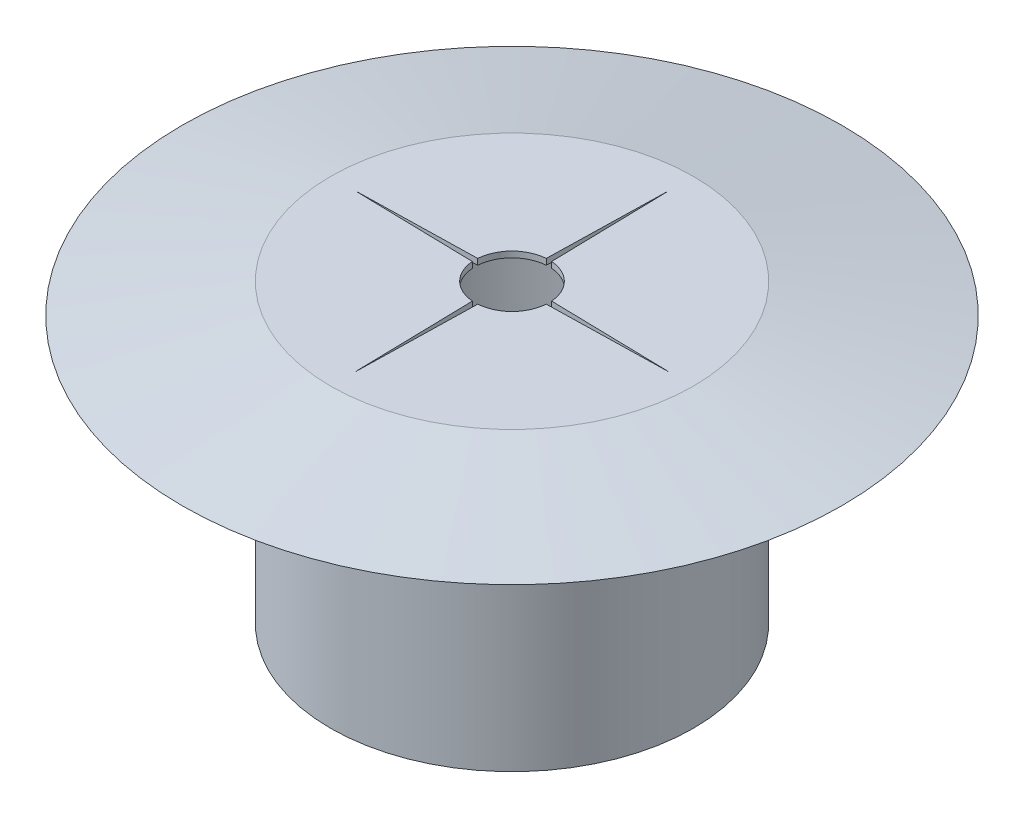
SolidWorks part; units mm, degrees
ref_plane "Alzado" through (0, 0, 0) normal (0, 0, 1) x (1, 0, 0)
ref_plane "Planta" through (0, 0, 0) normal (0, 1, 0) x (1, 0, 0)
ref_plane "Vista lateral" through (0, 0, 0) normal (1, 0, 0) x (0, 0, -1)
sketch "Croquis1" plane through (0, 0, 0) normal (0, 0, 1) x (1, 0, 0)
  line L0 (0, 0) -> (0, 16.2) construction
  line L1 (-10.9, 20) -> (-10.9, 0)
  line L2 (-10.9, 0) -> (-12.25, 0)
  line L3 (-12.25, 0) -> (-12.25, 18)
  line L4 (-12.25, 18) -> (-22.25, 18)
  line L5 (-22.25, 18) -> (-12.25, 20)
  line L6 (-12.25, 20) -> (-10.9, 20)
  dimension "D1" = 1.35
  dimension "D2" = 2
  dimension "D3" = 12.25
  dimension "D4" = 10
  dimension "D5" = 20
revolve "Revolución1" add sketch "Croquis1" angle 360 about L0
sketch "Croquis3" plane through (0, 20, 0) normal (0, 1, 0) x (1, 0, 0)
  line L0 (0, 0) -> (0, -10.9) construction
  line L2 (0, 0) -> (7.7075, -7.7075) construction
  line L4 (0, 0) -> (10.9, 0) construction
  line L5 (0.1813, -2.4934) -> (0, -10.6398)
  line L6 (2.4934, -0.1813) -> (10.6398, 0)
  line L7 (-0.1813, -2.4934) -> (0, -10.6398)
  line L8 (-2.4934, -0.1813) -> (-10.6398, 0)
  line L9 (-2.4934, 0.1813) -> (-10.6398, 0)
  line L10 (-0.1813, 2.4934) -> (0, 10.6398)
  line L11 (0.1813, 2.4934) -> (0, 10.6398)
  line L12 (2.4934, 0.1813) -> (10.6398, 0)
  circle A1 centre (0, 0) radius 2.5 construction
  arc A2 (2.4934, -0.1813) -> (0.1813, -2.4934) centre (0, 0) cw
  circle A3 centre (0, 0) radius 10.9 construction
  arc A4 (10.9, 0) -> (0, -10.9) centre (0, 0) cw
  arc A5 (0, -10.9) -> (-10.9, 0) centre (0, 0) cw
  arc A6 (-0.1813, -2.4934) -> (-2.4934, -0.1813) centre (0, 0) cw
  arc A7 (-10.9, 0) -> (0, 10.9) centre (0, 0) cw
  arc A8 (-2.4934, 0.1813) -> (-0.1813, 2.4934) centre (0, 0) cw
  arc A9 (0, 10.9) -> (10.9, 0) centre (0, 0) cw
  arc A10 (0.1813, 2.4934) -> (2.4934, 0.1813) centre (0, 0) cw
  point P15 (0.2901, -3.9895)
  dimension "D1" = 5
  dimension "D2" = 4
extrude "Saliente-Extruir2" add sketch "Croquis3" against normal blind 0.4 contours L5 L11 A10 L12 L6 A2 L7 A6 L8 L9 A8 L10
